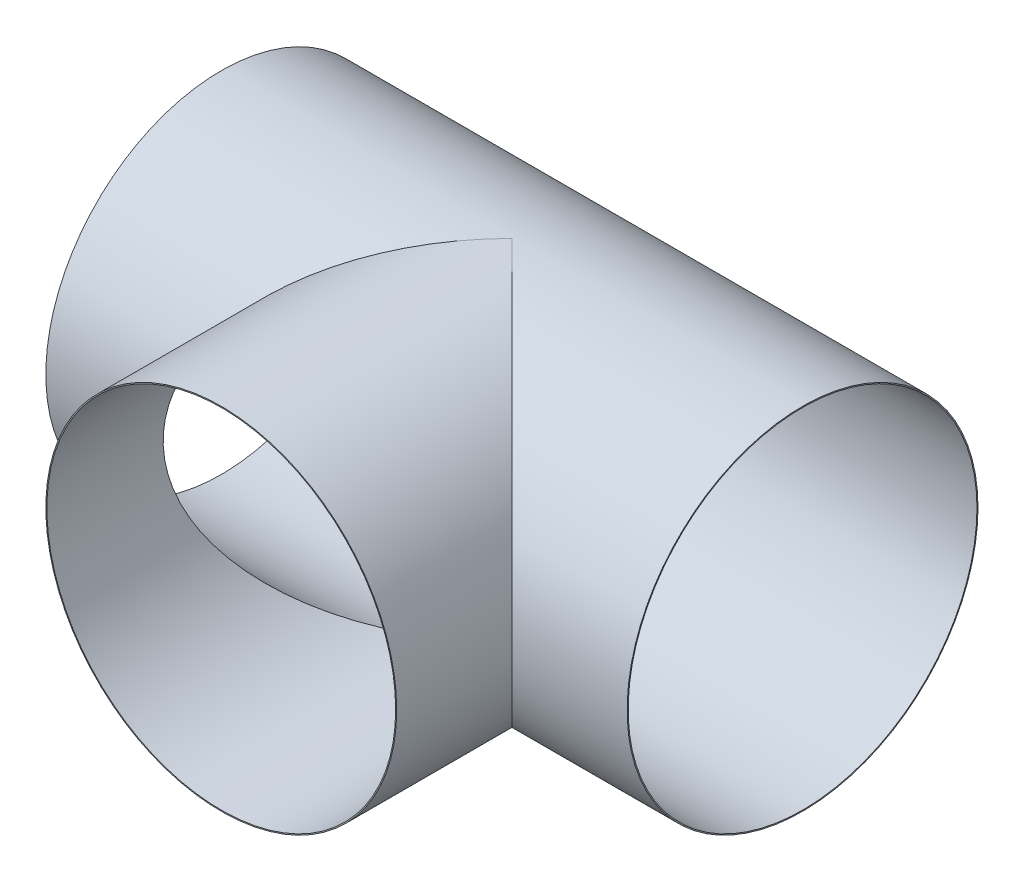
SolidWorks part; units mm, degrees
ref_plane "Front" through (0, 0, 0) normal (0, 0, 1) x (1, 0, 0)
ref_plane "Top" through (0, 0, 0) normal (0, 1, 0) x (1, 0, 0)
ref_plane "Right" through (0, 0, 0) normal (1, 0, 0) x (0, 0, -1)
sketch "Sketch1" plane through (0, 0, 0) normal (0, 0, 1) x (1, 0, 0)
  circle A0 centre (0, 0) radius 38.3273
  dimension "D1" = 76.6547
extrude "Boss-Extrude2" add sketch "Sketch1" against normal blind 63.5
ref_plane "Plane1" through (63.5, 0, 0) normal (1, 0, 0) x (0, 0, -1)
sketch "Sketch2" plane through (63.5, 0, 0) normal (1, 0, 0) x (0, 0, -1)
  line L0 (63.5, -38.3273) -> (63.5, 38.3273) construction
  circle A0 centre (63.5, 0) radius 38.3273
  dimension "D1" = 76.6547
extrude "Boss-Extrude3" add sketch "Sketch2" against normal blind 127
sketch "Sketch3" plane through (63.5, 0, 0) normal (1, 0, 0) x (0, 0, -1)
  circle A0 centre (63.5, 0) radius 38.1
  dimension "D1" = 76.2
extrude "Cut-Extrude1" cut sketch "Sketch3" against normal through all
sketch "Sketch4" plane through (0, 0, 0) normal (0, 0, 1) x (1, 0, 0)
  circle A0 centre (0, 0) radius 38.1
  dimension "D1" = 76.2
extrude "Cut-Extrude2" cut sketch "Sketch4" against normal blind 63.5
sketch "Sketch5" plane through (0, 0, 0) normal (0, 1, 0) x (1, 0, 0)
  line L0 (-63.5, 63.5) -> (63.5, 63.5) construction
  line L1 (-63.5, 101.8273) -> (-63.5, 25.1727) construction
  line L2 (63.5, -50) -> (63.5, 50) construction
  line L3 (0, 0) -> (0, 63.5) construction
